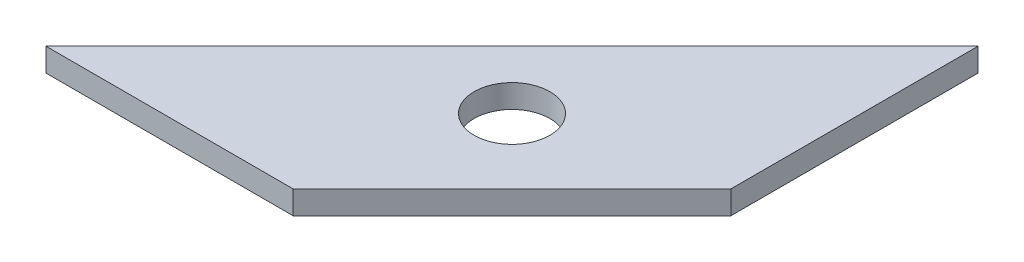
SolidWorks part; units mm, degrees
material "1023 Chapa de acero al carbono (SS)"
ref_plane "Alzado" through (0, 0, 0) normal (0, 0, 1) x (1, 0, 0)
ref_plane "Planta" through (0, 0, 0) normal (0, 1, 0) x (1, 0, 0)
ref_plane "Vista lateral" through (0, 0, 0) normal (1, 0, 0) x (0, 0, -1)
sketch "Sketch1" plane through (0, 0, 0) normal (0, 1, 0) x (1, 0, 0)
  line L0 (-40, 0) -> (-18.7868, 0)
  line L1 (-18.7868, 0) -> (0, 18.7868)
  line L2 (0, 18.7868) -> (0, 40)
  line L3 (0, 40) -> (-40, 0)
  dimension "D1" = 15
  dimension "D2" = 40
extrude "Extrude1" add sketch "Sketch1" along normal blind 2
hole_wizard "Ø6.5 (6.5) Diameter Hole1" positions "Sketch2" profile "Sketch3" hole size "Ø6.5" standard "ISO" end condition up to next
sketch "Sketch2" plane through (0, 2, 0) normal (0, 1, 0) x (1, 0, 0)
  line L0 (-40, 0) -> (-18.7868, 0) construction
  line L1 (0, 18.7868) -> (0, 40) construction
  point P0 (-15, 15)
  dimension "D1" = 15
  dimension "D2" = 15
sketch "Sketch3" plane through (-15, 2, -15) normal (1, 0, 0) x (0, 0, 1)
  line L0 (0, 0) -> (0, 2)
  line L1 (0, 2) -> (3.25, 2)
  line L2 (3.25, 2) -> (3.25, 0)
  line L5 (3.25, 0) -> (0, 0)
  line L11 (0, -6.35) -> (0, 107.95) construction
  dimension "Diámetro de taladro hasta el siguiente" = 6.5
  dimension "Profundidad de taladro hasta el siguiente" = 2
